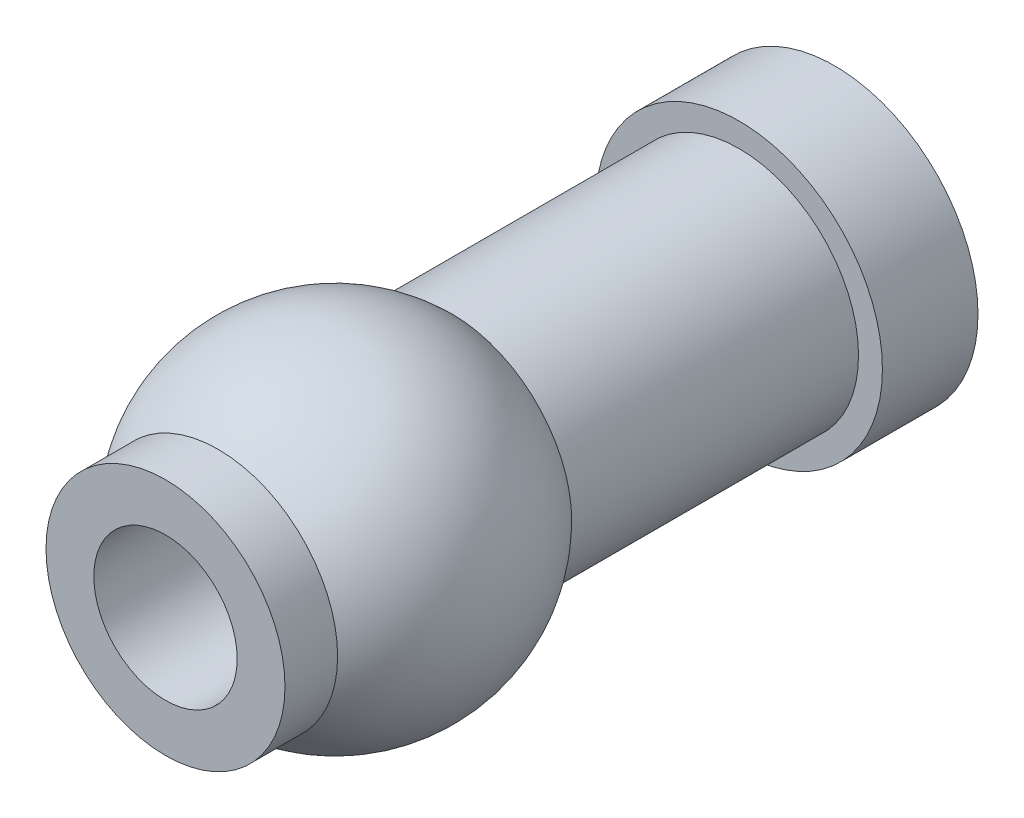
SolidWorks part; units mm, degrees
material "1060 Alloy"
ref_plane "Front Plane" through (0, 0, 0) normal (0, 0, 1) x (1, 0, 0)
ref_plane "Top Plane" through (0, 0, 0) normal (0, 1, 0) x (1, 0, 0)
ref_plane "Right Plane" through (0, 0, 0) normal (1, 0, 0) x (0, 0, -1)
sketch "Sketch1" plane through (0, 0, 0) normal (1, 0, 0) x (0, 0, -1)
  line L0 (0, 0) -> (14, 0) construction
  line L1 (14, 1.5) -> (0, 1.5)
  line L2 (14, 1.5) -> (14, 3)
  line L3 (14, 3) -> (12, 3)
  line L4 (12, 3) -> (12, 2.5)
  line L5 (12, 2.5) -> (6, 2.5)
  line L6 (0, 1.5) -> (0, 2.5)
  line L7 (0, 2.5) -> (1.101, 2.5)
  circle A0 centre (3.5505, 0) radius 3.5
  dimension "D3" = 7
  dimension "D1" = 1.5
  dimension "D2" = 14
  dimension "D4" = 3
  dimension "D5" = 2
  dimension "D6" = 6
  dimension "D7" = 2.5
  dimension "D8" = 0
  dimension "D9" = 2.5
revolve "Revolve1" add sketch "Sketch1" angle 360 about L0
